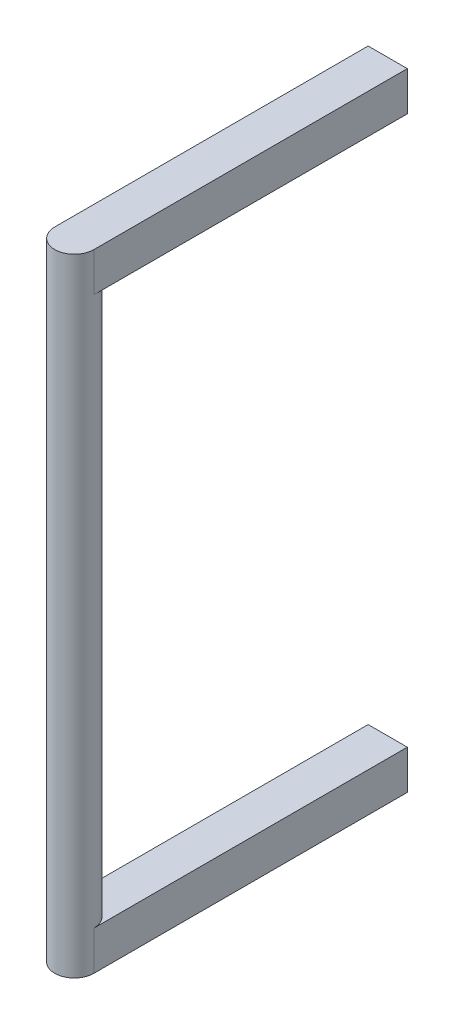
SolidWorks part; units mm, degrees
ref_plane "Front Plane" through (0, 0, 0) normal (0, 0, 1) x (1, 0, 0)
ref_plane "Top Plane" through (0, 0, 0) normal (0, 1, 0) x (1, 0, 0)
ref_plane "Right Plane" through (0, 0, 0) normal (1, 0, 0) x (0, 0, -1)
sketch "Sketch1" plane through (0, 0, 0) normal (0, 1, 0) x (1, 0, 0)
  circle A0 centre (0, 0) radius 12.7
  dimension "D1" = 25.4
extrude "Boss-Extrude1" add sketch "Sketch1" along normal blind 177.8
sketch "Sketch2" plane through (0, 177.8, 0) normal (0, 1, 0) x (1, 0, 0)
  line L0 (-12.7, 0) -> (-12.7, 203.2)
  line L1 (-12.7, 203.2) -> (12.7, 203.2)
  line L2 (12.7, 203.2) -> (12.7, 0)
  circle A0 centre (0, 0) radius 12.7 construction
  arc A1 (-12.7, 0) -> (12.7, 0) centre (0, 0) ccw
extrude "Boss-Extrude2" add sketch "Sketch2" along normal blind 25.4
ref_plane "Plane1" through (0, 0, 0) normal (0, -1, 0) x (-1, 0, 0)
mirror "Mirror1" about plane through (0, 0, 0) normal (0, -1, 0) of "Boss-Extrude1", "Boss-Extrude2"
